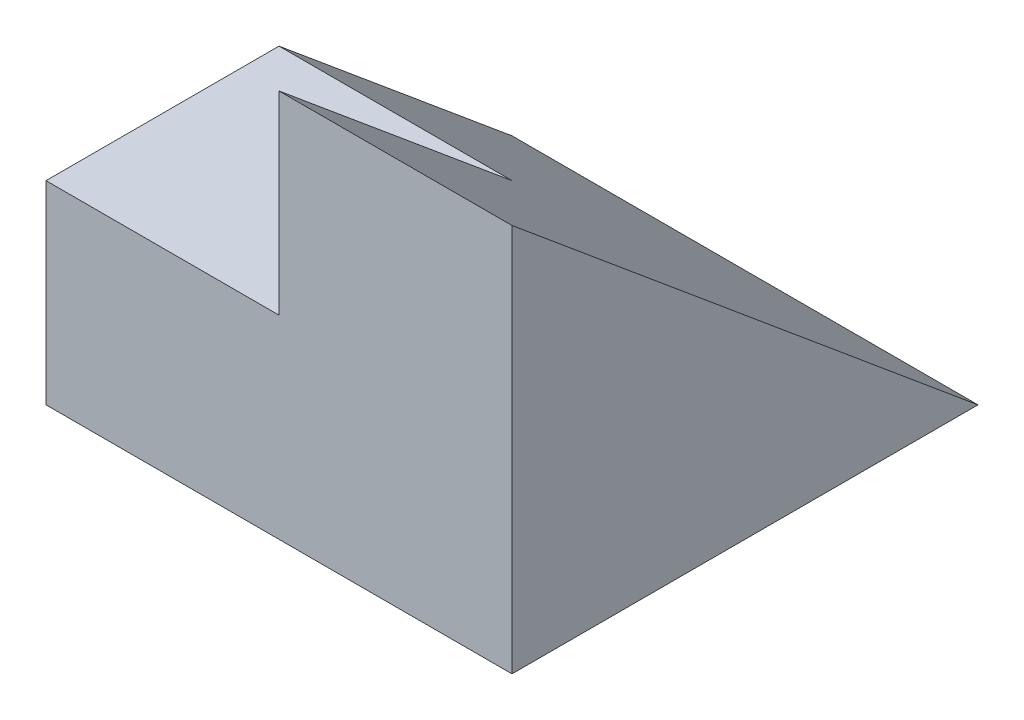
SolidWorks part; units mm, degrees
ref_plane "Front" through (0, 0, 0) normal (0, 0, 1) x (1, 0, 0)
ref_plane "Top" through (0, 0, 0) normal (0, 1, 0) x (1, 0, 0)
ref_plane "Right" through (0, 0, 0) normal (1, 0, 0) x (0, 0, -1)
sketch "Sketch1" plane through (0, 0, 0) normal (0, 1, 0) x (1, 0, 0)
  line L1 (-3, -3) -> (3, -3)
  line L2 (-3, -3) -> (-3, 3)
  line L3 (-3, 3) -> (3, 3)
  line L4 (3, -3) -> (3, 3)
  line L5 (-3, -3) -> (3, 3) construction
  line L6 (-3, 3) -> (3, -3) construction
  point P0 (0, 0)
  dimension "D1" = 6
  dimension "D2" = 6
extrude "Boss-Extrude1" add sketch "Sketch1" along normal blind 5
sketch "Sketch12" plane through (-3, 0, 0) normal (-1, 0, 0) x (0, 0, 1)
  line L0 (-3, 0) -> (3, 5)
  line L4 (-3, 0) -> (3, 0)
  line L5 (3, 0) -> (3, 5)
  line L6 (3, 5) -> (-3, 5)
  line L7 (-3, 5) -> (-3, 0)
  line L8 (-3, 0) -> (3, 0)
  line L9 (3, 0) -> (3, 5)
  line L10 (3, 5) -> (-3, 5)
  line L11 (-3, 5) -> (-3, 0)
  line M7 (3, 5) -> (-3, 5)
  line M8 (-3, 5) -> (-3, 0)
  dimension "D1" = 0
extrude "Cut-Extrude9" cut sketch "Sketch12" against normal blind 23.5 contours L0 M8 M7
sketch "Sketch13" plane through (-3, 0, 0) normal (-1, 0, 0) x (0, 0, 1)
  line L0 (0, 2.5) -> (3, 2.5)
  line L3 (3, 0) -> (3, 5)
  line L4 (3, 5) -> (-3, 0)
  line L5 (-3, 0) -> (3, 0)
  line L6 (3, 0) -> (3, 5)
  line L7 (3, 5) -> (-3, 0)
  line L8 (-3, 0) -> (3, 0)
  line M4 (3, 0) -> (3, 5)
  line M5 (3, 5) -> (-3, 0)
  dimension "D2" = 2.5
  dimension "D1" = 0
extrude "Cut-Extrude10" cut sketch "Sketch13" against normal blind 3 contours L0 M5 M4
